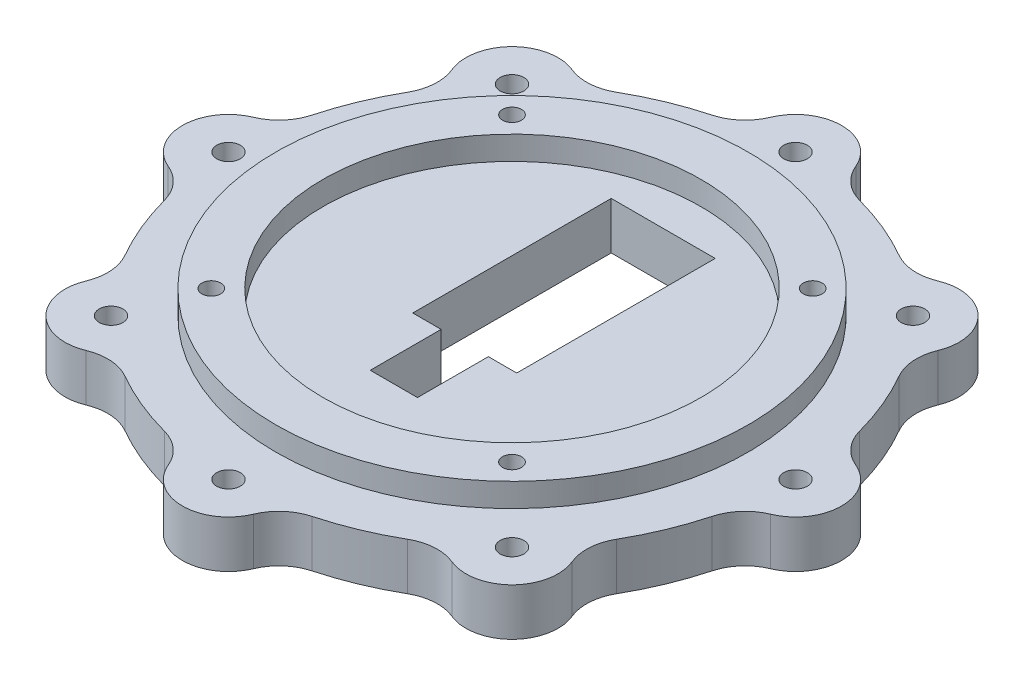
SolidWorks part; units mm, degrees
ref_plane "Alzado" through (0, 0, 0) normal (0, 0, 1) x (1, 0, 0)
ref_plane "Planta" through (0, 0, 0) normal (0, 1, 0) x (1, 0, 0)
ref_plane "Vista lateral" through (0, 0, 0) normal (1, 0, 0) x (0, 0, -1)
sketch "Croquis1" plane through (0, 0, 0) normal (0, 1, 0) x (1, 0, 0)
  line L0 (0, 0) -> (0, 75) construction
  line L1 (0, 0) -> (8.2936, 49.5609)
  line L2 (0, 0) -> (-8.2936, 49.5609)
  line L3 (0, 0) -> (40.9093, 29.1803)
  line L4 (0, 0) -> (29.1803, 40.9093)
  line L5 (0, 0) -> (49.5609, -8.2936)
  line L6 (0, 0) -> (49.5609, 8.2936)
  line L7 (0, 0) -> (29.1803, -40.9093)
  line L8 (0, 0) -> (40.9093, -29.1803)
  line L9 (0, 0) -> (-8.2936, -49.5609)
  line L10 (0, 0) -> (8.2936, -49.5609)
  line L11 (0, 0) -> (-40.9093, -29.1803)
  line L12 (0, 0) -> (-29.1803, -40.9093)
  line L13 (0, 0) -> (-49.5609, 8.2936)
  line L14 (0, 0) -> (-49.5609, -8.2936)
  line L15 (0, 0) -> (-29.1803, 40.9093)
  line L16 (0, 0) -> (-40.9093, 29.1803)
  line L17 (0, 0) -> (0, -82.5226) construction
  line L18 (-11, 32) -> (11, 32)
  line L19 (-11, 32) -> (-11, -10)
  line L20 (-11, -10) -> (11, -10)
  line L21 (11, 32) -> (11, -10)
  line L22 (-11, 32) -> (11, -10) construction
  line L23 (-11, -10) -> (11, 32) construction
  line L24 (0, 0) -> (42.4264, 42.4264) construction
  circle A1 centre (0, 0) radius 50.25
  circle A2 centre (0, 0) radius 39.75
  circle A3 centre (0, -60) radius 2.5
  circle A4 centre (-42.4264, -42.4264) radius 2.5
  circle A5 centre (-60, 0) radius 2.5
  circle A6 centre (-42.4264, 42.4264) radius 2.5
  circle A7 centre (0, 60) radius 2.5
  circle A8 centre (42.4264, 42.4264) radius 2.5
  circle A9 centre (60, 0) radius 2.5
  circle A10 centre (42.4264, -42.4264) radius 2.5
  circle A11 centre (31.8198, 31.8198) radius 2
  circle A12 centre (31.8198, -31.8198) radius 2
  circle A13 centre (-31.8198, -31.8198) radius 2
  circle A14 centre (-31.8198, 31.8198) radius 2
  circle A15 centre (0, 0) radius 60
  circle A16 centre (0, -60) radius 9.75
  circle A17 centre (-42.4264, -42.4264) radius 9.75
  circle A18 centre (-60, 0) radius 9.75
  circle A19 centre (-42.4264, 42.4264) radius 9.75
  circle A20 centre (0, 60) radius 9.75
  circle A21 centre (42.4264, 42.4264) radius 9.75
  circle A22 centre (60, 0) radius 9.75
  circle A23 centre (42.4264, -42.4264) radius 9.75
  point P5 (0, 11)
  point P25 (0, 0)
  point P48 (0, 0)
  point P57 (0, 0)
  point P74 (0, 0)
  dimension "D2" = 100.5
  dimension "D3" = 79.5
  dimension "D10" = 5
  dimension "D14" = 4
  dimension "D17" = 120
  dimension "D18" = 8
  dimension "D4" = 9.5
  dimension "D5" = 9.5
  dimension "D7" = 42
  dimension "D8" = 22
  dimension "D9" = 10
  dimension "D11" = 60
  dimension "D13" = 45
  dimension "D15" = 45
  dimension "D6" = 8
  dimension "D12" = 8
  dimension "D16" = 4
extrude "Saliente-Extruir1" add sketch "Croquis1" along normal blind 10
fillet "Redondeo1" radius 10 16 edges at (34.9947, 5, -48.7377) (48.7377, 5, -34.9947) (59.2078, 5, -9.7178) (59.2078, 5, 9.7178) (48.7377, 5, 34.9947) (34.9947, 5, 48.7377) (9.7178, 5, 59.2078) (-9.7178, 5, 59.2078) (-34.9947, 5, 48.7377) (-48.7377, 5, 34.9947) (-59.2078, 5, 9.7178) (-59.2078, 5, -9.7178) (-48.7377, 5, -34.9947) (-34.9947, 5, -48.7377) (-9.7178, 5, -59.2078) (9.7178, 5, -59.2078)
sketch "Croquis2" plane through (0, 0, 0) normal (0, -1, 0) x (1, 0, 0)
  circle A0 centre (31.8198, 31.8198) radius 5
  circle A1 centre (31.8198, -31.8198) radius 5
  circle A2 centre (-31.8198, -31.8198) radius 5
  circle A3 centre (-31.8198, 31.8198) radius 5
  point P13 (0, 0)
  dimension "D1" = 10
  dimension "D2" = 4
extrude "Cortar-Extruir1" cut sketch "Croquis2" against normal blind 5
sketch "Croquis3" plane through (0, 10, 0) normal (0, 1, 0) x (1, 0, 0)
  line L0 (-11, -10) -> (11, -10) construction
  line L1 (-5, -10) -> (5, -10)
  line L2 (-5, -10) -> (-5, -25)
  line L3 (-5, -25) -> (5, -25)
  line L4 (5, -10) -> (5, -25)
  point P6 (5, -17.5)
  dimension "D1" = 5
  dimension "D2" = 5
  dimension "D3" = 15
extrude "Cortar-Extruir2" cut sketch "Croquis3" against normal blind 10
sketch "Croquis4" plane through (0, 10, 0) normal (0, 1, 0) x (1, 0, 0)
  circle A0 centre (0, 0) radius 50
  circle A1 centre (0, 0) radius 40
  circle A2 centre (-31.8198, 31.8198) radius 2
  circle A3 centre (31.8198, 31.8198) radius 2
  circle A4 centre (31.8198, -31.8198) radius 2
  circle A5 centre (-31.8198, -31.8198) radius 2
  dimension "D1" = 100
  dimension "D2" = 80
extrude "Saliente-Extruir2" add sketch "Croquis4" along normal blind 5
